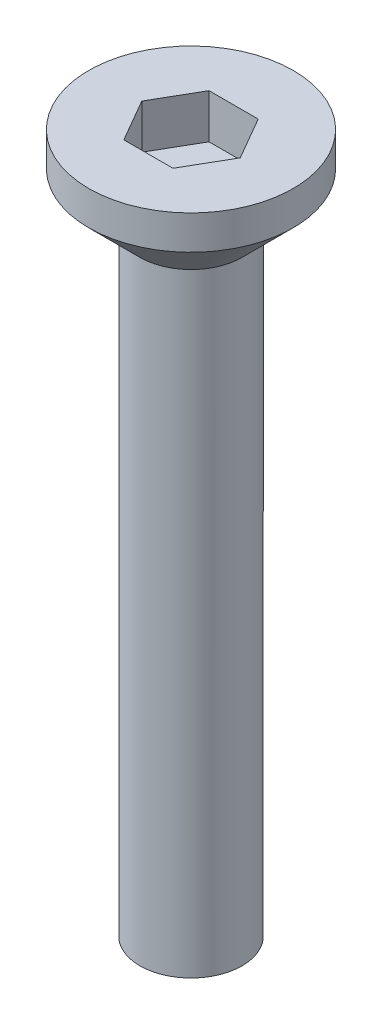
SolidWorks part; units mm, degrees
material "AISI 304"
ref_plane "前视基准面" through (0, 0, 0) normal (0, 0, 1) x (1, 0, 0)
ref_plane "上视基准面" through (0, 0, 0) normal (0, 1, 0) x (1, 0, 0)
ref_plane "右视基准面" through (0, 0, 0) normal (1, 0, 0) x (0, 0, -1)
sketch "草图1" plane through (0, 0, 0) normal (0, 1, 0) x (1, 0, 0)
  circle A0 centre (0, 0) radius 3
  dimension "D1" = 6
extrude "沉头头" add sketch "草图1" along normal blind 2.5
chamfer "倒角1" distance 1.5 angle 45 1 edges at (0, 0, 3)
sketch "草图2" plane through (0, 2.5, 0) normal (0, 1, 0) x (1, 0, 0)
  line L1 (1.4434, 0) -> (0.7217, 1.25)
  line L2 (0.7217, 1.25) -> (-0.7217, 1.25)
  line L3 (-0.7217, 1.25) -> (-1.4434, 0)
  line L4 (-1.4434, 0) -> (-0.7217, -1.25)
  line L5 (-0.7217, -1.25) -> (0.7217, -1.25)
  line L6 (0.7217, -1.25) -> (1.4434, 0)
  circle A0 centre (0, 0) radius 1.25 construction
  dimension "D1" = 2.5
extrude "内六角口" cut sketch "草图2" against normal blind 1.3
sketch "草图3" plane through (0, 0, 0) normal (0, -1, 0) x (1, 0, 0)
  circle A0 centre (0, 0) radius 1.5
  dimension "D1" = 3
extrude "螺纹长" add sketch "草图3" along normal blind 18
